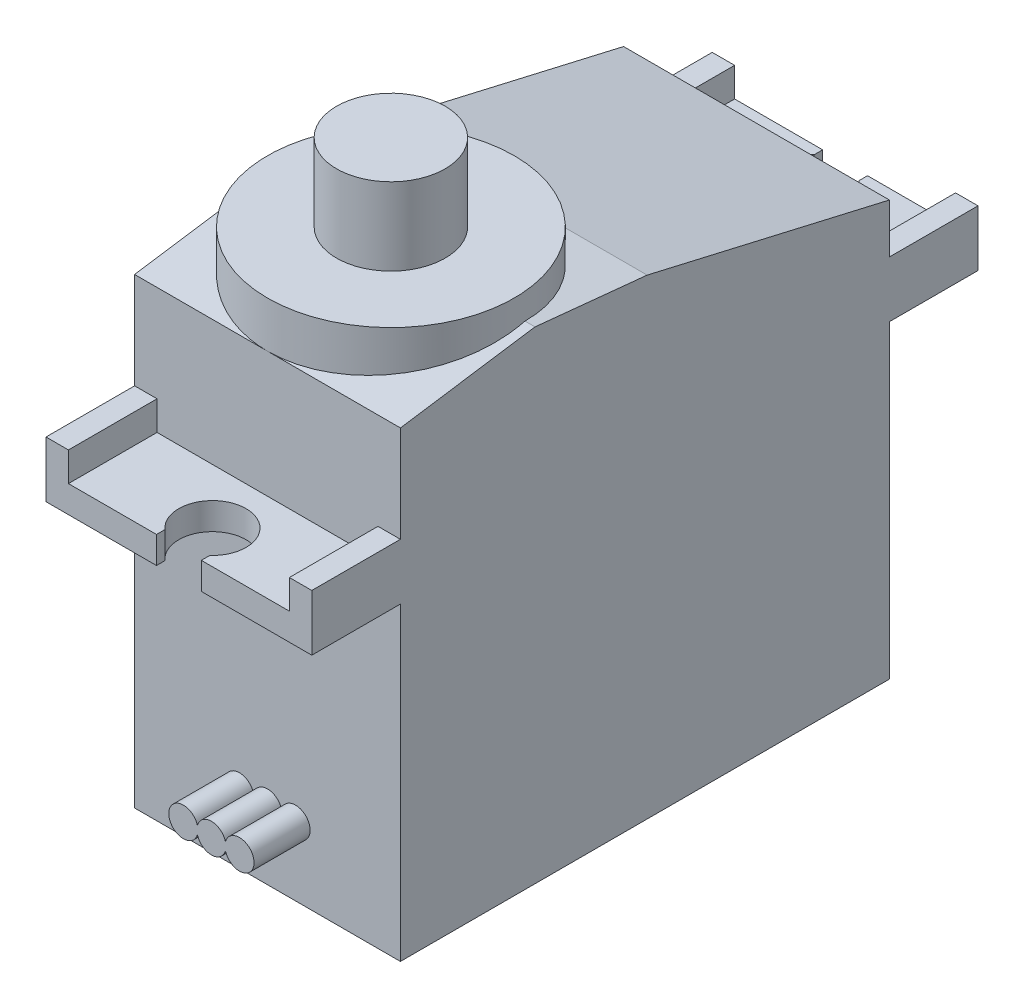
SolidWorks part; units mm, degrees
ref_plane "Front Plane" through (0, 0, 0) normal (0, 0, 1) x (1, 0, 0)
ref_plane "Top Plane" through (0, 0, 0) normal (0, 1, 0) x (1, 0, 0)
ref_plane "Right Plane" through (0, 0, 0) normal (1, 0, 0) x (0, 0, -1)
sketch "Sketch2" plane through (0, 0, 0) normal (0, 1, 0) x (1, 0, 0)
  line L1 (-5.925, -10.9) -> (5.925, -10.9)
  line L2 (-5.925, -10.9) -> (-5.925, 10.9)
  line L3 (-5.925, 10.9) -> (5.925, 10.9)
  line L4 (5.925, -10.9) -> (5.925, 10.9)
  line L5 (-5.925, -10.9) -> (5.925, 10.9) construction
  line L6 (-5.925, 10.9) -> (5.925, -10.9) construction
  point P0 (0, 0)
  dimension "D1" = 11.85
  dimension "D2" = 21.8
extrude "Boss-Extrude1" add sketch "Sketch2" against normal blind 13.8
sketch "Sketch3" plane through (0, 0, 0) normal (0, 1, 0) x (1, 0, 0)
  line L0 (5.925, -10.9) -> (5.925, 10.9) construction
  line L1 (-5.925, -14.85) -> (5.925, -14.85)
  line L2 (-5.925, -14.85) -> (-5.925, 14.85)
  line L3 (-5.925, 14.85) -> (5.925, 14.85)
  line L4 (5.925, -14.85) -> (5.925, 14.85)
  line L5 (-5.925, -14.85) -> (5.925, 14.85) construction
  line L6 (-5.925, 14.85) -> (5.925, -14.85) construction
  point P0 (0, 0)
  dimension "D1" = 29.7
extrude "Boss-Extrude2" add sketch "Sketch3" along normal blind 1.2
sketch "Sketch4" plane through (0, 1.2, 0) normal (0, 1, 0) x (1, 0, 0)
  line L0 (0, 0) -> (7.7235, 0) construction
  circle A0 centre (0, 13.355) radius 1.5
  circle A1 centre (0, -13.355) radius 1.5
  dimension "D1" = 3
  dimension "D2" = 23.71
extrude "Cut-Extrude11" cut sketch "Sketch4" against normal blind 1.2
sketch "Sketch5" plane through (0, 1.2, 0) normal (0, 1, 0) x (1, 0, 0)
  line L0 (0, 0) -> (0, 10.2797) construction
  line L1 (-1, 15.85) -> (1, 15.85)
  line L2 (-1, 15.85) -> (-1, 13.85)
  line L3 (-1, 13.85) -> (1, 13.85)
  line L4 (1, 15.85) -> (1, 13.85)
  line L5 (-1, -13.85) -> (1, -13.85)
  line L6 (-1, -13.85) -> (-1, -15.85)
  line L7 (-1, -15.85) -> (1, -15.85)
  line L8 (1, -13.85) -> (1, -15.85)
  line L9 (0, 0) -> (3.8506, 0) construction
  line L10 (5.925, -14.85) -> (2.1573, -14.85) construction
  line L11 (0.1224, -14.85) -> (5.925, -14.85) construction
  dimension "D1" = 2
  dimension "D2" = 2
extrude "Cut-Extrude12" cut sketch "Sketch5" against normal blind 1.2
sketch "Sketch6" plane through (0, 1.2, 0) normal (0, 1, 0) x (1, 0, 0)
  line L0 (-5.925, -10.9) -> (5.925, -10.9) construction
  circle A0 centre (0, -5.4) radius 2.42 construction
  circle A1 centre (0, -5.4) radius 5.5
  dimension "D1" = 4.84
  dimension "D2" = 11
extrude "Boss-Extrude3" add sketch "Sketch6" along normal offset from surface (7.65 mm away) 22.65 up to face at (0, -13.8, 0)
sketch "Sketch7" plane through (0, 8.85, 0) normal (0, 1, 0) x (1, 0, 0)
  circle A0 centre (0, -5.4) radius 2.42
  circle A1 centre (0, -5.4) radius 2.42 construction
extrude "Boss-Extrude4" add sketch "Sketch7" along normal offset from surface (3.45 mm away) 26.1 up to face at (0, -13.8, 0)
sketch "Sketch8" plane through (5.925, 0, 0) normal (1, 0, 0) x (0, 0, -1)
  line L0 (-10.9, 1.2) -> (-10.9, 6.8)
  line L1 (-10.9, 8.85) -> (-10.9, 1.2) construction
  line L2 (-10.9, 6.8) -> (-4.9, 7.7)
  line L3 (-4.9, 7.7) -> (0.1, 7.2)
  line L4 (0.1, 7.2) -> (10.9, 4.7)
  line L5 (10.9, 4.7) -> (10.9, 1.2)
  line L6 (-14.85, 1.2) -> (14.85, 1.2) construction
  line L7 (10.9, 1.2) -> (-10.9, 1.2)
  line L8 (-10.9, -13.8) -> (10.9, -13.8) construction
  line L9 (10.9, -13.8) -> (10.9, 0) construction
  line L10 (0.1, 1.2) -> (0.1, 8.85) construction
  dimension "D1" = 20.6
  dimension "D2" = 21.5
  dimension "D3" = 6
  dimension "D4" = 18.5
  dimension "D5" = 0.5
extrude "Boss-Extrude5" add sketch "Sketch8" against normal up to surface (11.85 mm away) up to face at (-5.925, -4.875, -0.4938)
sketch "Sketch9" plane through (0, 1.2, 0) normal (0, 1, 0) x (1, 0, 0)
  line L0 (0, -10.9) -> (5.925, -10.9) construction
  line L1 (5.925, -14.85) -> (4.925, -14.85)
  line L2 (5.925, -14.85) -> (5.925, -10.9)
  line L3 (5.925, -10.9) -> (4.925, -10.9)
  line L4 (4.925, -14.85) -> (4.925, -10.9)
  line L5 (-5.925, -10.9) -> (5.925, -10.9) construction
  line L6 (-5.925, -14.85) -> (-4.925, -14.85)
  line L7 (-5.925, -14.85) -> (-5.925, -10.9)
  line L8 (-5.925, -10.9) -> (-4.925, -10.9)
  line L9 (-4.925, -14.85) -> (-4.925, -10.9)
  line L10 (-5.925, 10.9) -> (5.925, 10.9) construction
  line L11 (-5.925, 14.85) -> (-4.925, 14.85)
  line L12 (-5.925, 14.85) -> (-5.925, 10.9)
  line L13 (-5.925, 10.9) -> (-4.925, 10.9)
  line L14 (-4.925, 14.85) -> (-4.925, 10.9)
  line L16 (5.925, 14.85) -> (4.925, 14.85)
  line L17 (5.925, 14.85) -> (5.925, 10.9)
  line L18 (5.925, 10.9) -> (4.925, 10.9)
  line L19 (4.925, 14.85) -> (4.925, 10.9)
  dimension "D1" = 1
extrude "Boss-Extrude6" add sketch "Sketch9" along normal offset from surface (1.3 mm away) 2.5 up to face at (1.2313, 0, -13.7683)
sketch "Sketch10" plane through (0, 0, 10.9) normal (0, 0, 1) x (1, 0, 0)
  line L0 (0, -13.8) -> (0, -3.6759) construction
  line L1 (-1.9, -10.1) -> (1.9, -10.1) construction
  line L2 (-1.9, -10.1) -> (-1.9, -11.4) construction
  line L3 (-1.9, -11.4) -> (1.9, -11.4) construction
  line L4 (1.9, -10.1) -> (1.9, -11.4) construction
  line L5 (-5.925, -13.8) -> (5.925, -13.8) construction
  arc A0 (-0.625, -10.9285) -> (0.625, -10.9285) centre (0, -10.75) ccw
  arc A1 (0.625, -10.9285) -> (0.625, -10.5715) centre (1.25, -10.75) ccw
  arc A2 (-0.625, -10.5715) -> (-0.625, -10.9285) centre (-1.25, -10.75) ccw
  arc A3 (0.625, -10.5715) -> (-0.625, -10.5715) centre (0, -10.75) ccw
  dimension "D1" = 3.8
  dimension "D2" = 1.3
  dimension "D3" = 3.7
extrude "Boss-Extrude7" add sketch "Sketch10" along normal blind 2.5
